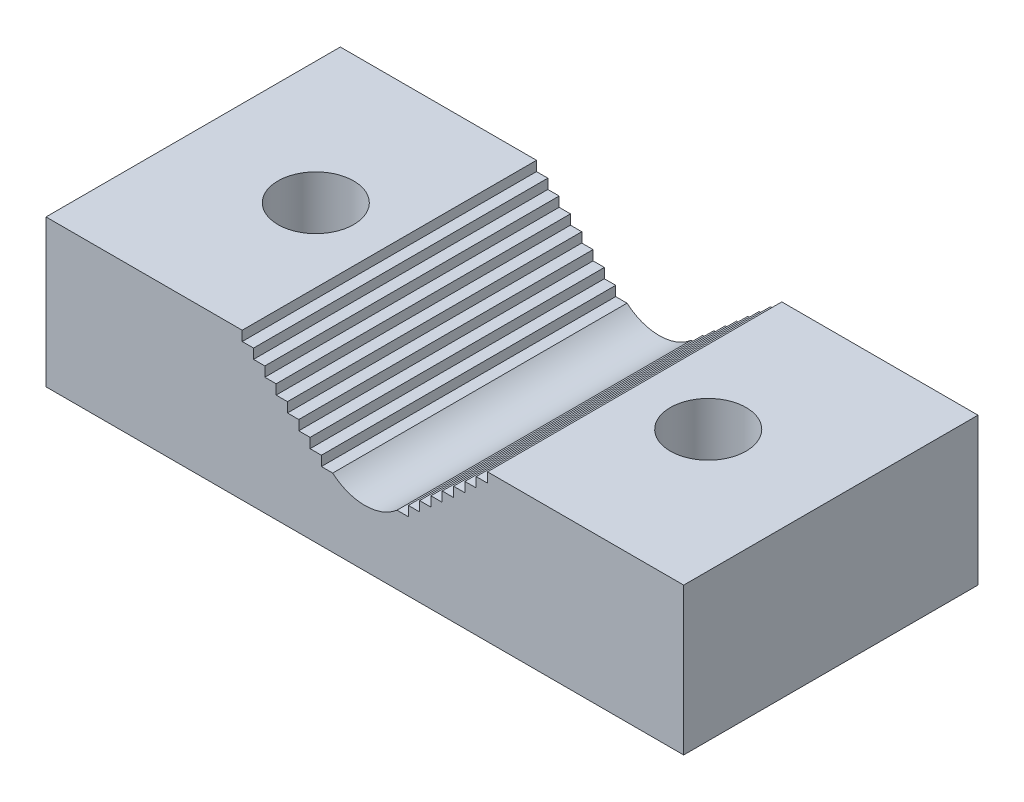
SolidWorks part; units mm, degrees
material "6061-T6 (SS)"
ref_plane "Front Plane" through (0, 0, 0) normal (0, 0, 1) x (1, 0, 0)
ref_plane "Top Plane" through (0, 0, 0) normal (0, 1, 0) x (1, 0, 0)
ref_plane "Right Plane" through (0, 0, 0) normal (1, 0, 0) x (0, 0, -1)
sketch "Sketch1" plane through (0, 0, 0) normal (0, 0, 1) x (1, 0, 0)
  line L0 (-34.925, 0) -> (34.925, 0)
  line L1 (34.925, 0) -> (34.925, 19.05)
  line L2 (34.925, 19.05) -> (-34.925, 19.05)
  line L3 (-34.925, 19.05) -> (-34.925, 0)
  point P3 (0, 0)
  dimension "D1" = 19.05
  dimension "D2" = 69.85
extrude "Boss-Extrude1" add sketch "Sketch1" against normal blind 38.1
sketch "Sketch2" plane through (0, 0, 0) normal (0, 0, 1) x (1, 0, 0)
  line L0 (-15.875, 19.05) -> (-4.1606, 8.89) construction
  line L1 (-15.875, 19.05) -> (0, 19.05)
  line L2 (34.925, 19.05) -> (-34.925, 19.05) construction
  line L3 (15.875, 19.05) -> (4.1606, 8.89) construction
  line L4 (15.875, 19.05) -> (0, 19.05)
  line L5 (-15.875, 19.05) -> (-15.875, 17.78)
  line L6 (-15.875, 17.78) -> (-14.4107, 17.78)
  line L7 (-14.4107, 17.78) -> (-14.4107, 16.51)
  line L8 (-14.4107, 16.51) -> (-12.9464, 16.51)
  line L9 (-12.9464, 16.51) -> (-12.9464, 15.24)
  line L10 (-12.9464, 15.24) -> (-11.4821, 15.24)
  line L11 (-11.4821, 15.24) -> (-11.4821, 13.97)
  line L12 (-11.4821, 13.97) -> (-10.0178, 13.97)
  line L13 (-10.0178, 13.97) -> (-10.0178, 12.7)
  line L14 (-10.0178, 12.7) -> (-8.5535, 12.7)
  line L15 (-8.5535, 12.7) -> (-8.5535, 11.43)
  line L16 (-8.5535, 11.43) -> (-7.0892, 11.43)
  line L17 (-7.0892, 11.43) -> (-7.0892, 10.16)
  line L18 (-7.0892, 10.16) -> (-5.6249, 10.16)
  line L19 (-5.6249, 10.16) -> (-5.6249, 8.89)
  line L20 (-5.6249, 8.89) -> (-4.1606, 8.89)
  line L21 (0, 19.05) -> (0, 0) construction
  line L24 (5.6249, 8.89) -> (4.1606, 8.89)
  line L25 (5.6249, 10.16) -> (5.6249, 8.89)
  line L26 (7.0892, 10.16) -> (5.6249, 10.16)
  line L27 (7.0892, 11.43) -> (7.0892, 10.16)
  line L28 (8.5535, 11.43) -> (7.0892, 11.43)
  line L29 (8.5535, 12.7) -> (8.5535, 11.43)
  line L30 (10.0178, 12.7) -> (8.5535, 12.7)
  line L31 (10.0178, 13.97) -> (10.0178, 12.7)
  line L32 (11.4821, 13.97) -> (10.0178, 13.97)
  line L33 (11.4821, 15.24) -> (11.4821, 13.97)
  line L34 (12.9464, 15.24) -> (11.4821, 15.24)
  line L35 (12.9464, 16.51) -> (12.9464, 15.24)
  line L36 (14.4107, 16.51) -> (12.9464, 16.51)
  line L37 (14.4107, 17.78) -> (14.4107, 16.51)
  line L38 (15.875, 17.78) -> (14.4107, 17.78)
  line L39 (15.875, 19.05) -> (15.875, 17.78)
  arc A0 (4.1606, 8.89) -> (-4.1606, 8.89) centre (0, 13.6871) cw
  point P7 (0, 19.05)
  dimension "D1" = 6.35
  dimension "D2" = 31.75
  dimension "D4" = 1.27
extrude "Cut-Extrude1" cut sketch "Sketch2" against normal up to next
sketch "Sketch3" plane through (0, 0, 0) normal (0, 0, 1) x (1, 0, 0)
  circle A0 centre (0, 24.151) radius 14.2875
  dimension "D1" = 28.575
hole_wizard "3/8 Clearance Hole1" positions "Sketch6" profile "Sketch5" hole size "3/8" standard "ANSI Inch" end condition through all
sketch "Sketch6" plane through (0, 19.05, 0) normal (0, 1, 0) x (1, 0, 0)
  line L0 (-15.875, 38.1) -> (-34.925, 38.1) construction
  line L1 (-34.925, 38.1) -> (-34.925, 0) construction
  line L2 (34.925, 38.1) -> (15.875, 38.1) construction
  line L3 (34.925, 38.1) -> (34.925, 0) construction
  point P0 (-25.4, 19.05)
  point P2 (25.4, 19.05)
  point P7 (-25.4, 38.1)
  point P10 (-34.925, 19.05)
  point P13 (25.4, 38.1)
  point P16 (34.925, 19.05)
sketch "Sketch5" plane through (-25.4, 19.05, -19.05) normal (1, 0, 0) x (0, 0, 1)
  line L0 (0, 0) -> (0, 19.05)
  line L1 (0, 19.05) -> (4.9022, 19.05)
  line L2 (4.9022, 19.05) -> (4.9022, 0)
  line L5 (4.9022, 0) -> (0, 0)
  line L11 (0, -6.35) -> (0, 107.95) construction
  dimension "Thru Hole Dia." = 9.8044
  dimension "Thru Hole Depth" = 19.05
sketch "Sketch7" plane through (0, 19.05, 0) normal (0, 1, 0) x (1, 0, 0)
  line L0 (-34.925, 38.1) -> (-41.275, 38.1)
  line L1 (-41.275, 38.1) -> (-41.275, 0)
  line L2 (-41.275, 0) -> (-32.3716, 0)
  line L3 (-15.875, 0) -> (-34.925, 0) construction
  line L4 (-32.3716, 0) -> (-32.3716, 38.1)
  line L5 (-15.875, 38.1) -> (-34.925, 38.1) construction
  line L6 (-32.3716, 38.1) -> (-34.925, 38.1)
  line L7 (0, 0) -> (0, 45.7584) construction
  line L8 (41.275, 0) -> (32.3716, 0)
  line L9 (41.275, 38.1) -> (41.275, 0)
  line L10 (34.925, 38.1) -> (41.275, 38.1)
  line L11 (32.3716, 0) -> (32.3716, 38.1)
  line L12 (32.3716, 38.1) -> (34.925, 38.1)
  dimension "D1" = 6.35
extrude "Boss-Extrude2" add sketch "Sketch7" against normal up to surface (19.05 mm away) up to face at (-25.4, 0, -14.1478)
